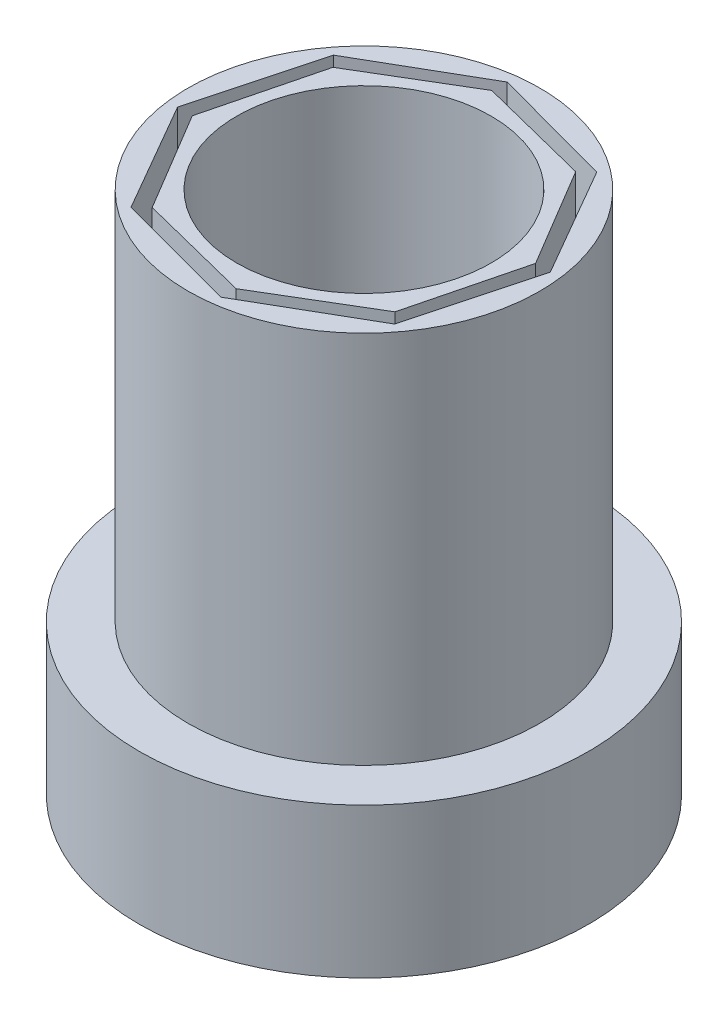
SolidWorks part; units mm, degrees
ref_plane "Front Plane" through (0, 0, 0) normal (0, 0, 1) x (1, 0, 0)
ref_plane "Top Plane" through (0, 0, 0) normal (0, 1, 0) x (1, 0, 0)
ref_plane "Right Plane" through (0, 0, 0) normal (1, 0, 0) x (0, 0, -1)
sketch "Sketch1" plane through (0, 0, 0) normal (0, 1, 0) x (1, 0, 0)
  line L31 (16.2132, -12.0711) -> (20, 2.9289)
  line L32 (20, 2.9289) -> (12.0711, 16.2132)
  line L33 (12.0711, 16.2132) -> (-2.9289, 20)
  line L34 (-2.9289, 20) -> (-16.2132, 12.0711)
  line L35 (-16.2132, 12.0711) -> (-20, -2.9289)
  line L36 (-20, -2.9289) -> (-12.0711, -16.2132)
  line L37 (-12.0711, -16.2132) -> (2.9289, -20)
  line L38 (2.9289, -20) -> (16.2132, -12.0711)
  circle A0 centre (0, 0) radius 17
  circle A2 centre (0, 0) radius 20.2133 construction
  point P3 (0, 0)
  dimension "D1" = 15
  dimension "D2" = 34
  dimension "D3" = 20
extrude "Boss-Extrude2" add sketch "Sketch1" along normal blind 50
sketch "Sketch3" plane through (0, 0, 0) normal (0, 1, 0) x (1, 0, 0)
  line L17 (-2.8902, 22) -> (-17.6001, 13.5126)
  line L18 (-17.6001, 13.5126) -> (-22, -2.8902)
  line L19 (-22, -2.8902) -> (-13.5126, -17.6001)
  line L20 (-13.5126, -17.6001) -> (2.8902, -22)
  line L21 (2.8902, -22) -> (17.6001, -13.5126)
  line L22 (17.6001, -13.5126) -> (22, 2.8902)
  line L23 (22, 2.8902) -> (13.5126, 17.6001)
  line L24 (13.5126, 17.6001) -> (-2.8902, 22)
  circle A0 centre (0, 0) radius 20.5 construction
  circle A1 centre (0, 0) radius 23.5
  point P1 (0, 0)
  dimension "D1" = 22
  dimension "D3" = 47
  dimension "D2" = 16.4029
extrude "Boss-Extrude4" add sketch "Sketch3" along normal blind 50 separate body
sketch "Sketch8" plane through (0, 0, 0) normal (0, 1, 0) x (1, 0, 0)
  circle A0 centre (0, 0) radius 30
  point P2 (0, 0)
  point P3 (0, 0)
  point P4 (0, 0)
  dimension "D1" = 60
extrude "Boss-Extrude5" add sketch "Sketch8" against normal blind 20
